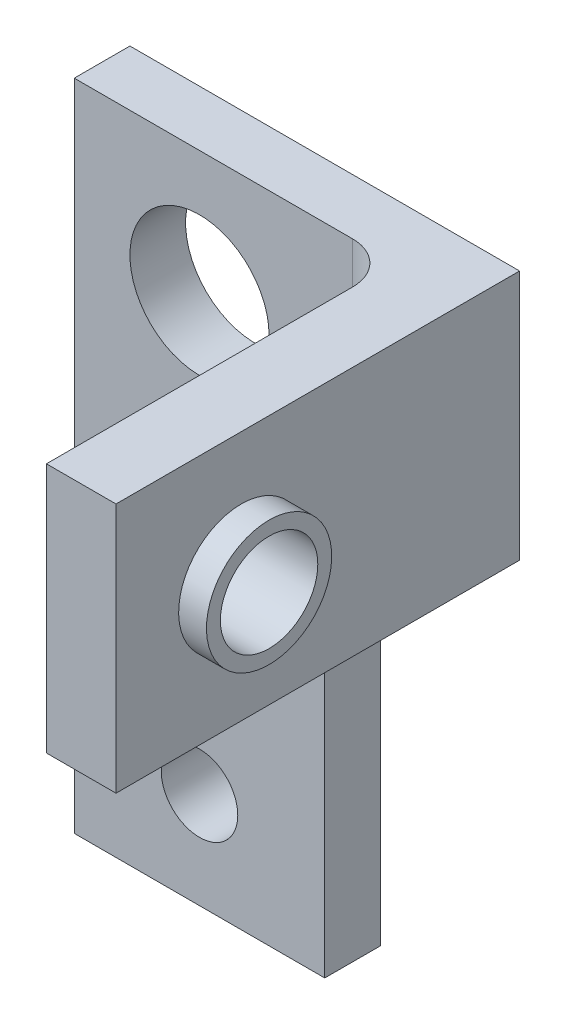
SolidWorks part; units mm, degrees
ref_plane "Front Plane" through (0, 0, 0) normal (0, 0, 1) x (1, 0, 0)
ref_plane "Top Plane" through (0, 0, 0) normal (0, 1, 0) x (1, 0, 0)
ref_plane "Right Plane" through (0, 0, 0) normal (1, 0, 0) x (0, 0, -1)
sketch "Sketch1" plane through (0, 0, 0) normal (0, 0, 1) x (1, 0, 0)
  line L1 (-4.5, 11) -> (4.5, 11)
  line L2 (-4.5, 11) -> (-4.5, -11)
  line L3 (-4.5, -11) -> (4.5, -11)
  line L4 (4.5, 11) -> (4.5, -11)
  point P0 (0, 0)
  dimension "D1" = 22
  dimension "D2" = 9
extrude "Boss-Extrude1" add sketch "Sketch1" along normal blind 2
sketch "Sketch3" plane through (0, 0, 2) normal (0, 0, 1) x (1, 0, 0)
  line L1 (-4.5, -11) -> (4.5, -11) construction
  line L2 (4.5, 11) -> (-4.5, 11) construction
  circle A0 centre (0, 6.5) radius 2.5
  circle A1 centre (0, -9) radius 1.375
  dimension "D1" = 5
  dimension "D2" = 2.75
  dimension "D3" = 2
  dimension "D4" = 4.5
extrude "Cut-Extrude1" cut sketch "Sketch3" against normal blind 2
sketch "Sketch4" plane through (4.5, 0, 0) normal (1, 0, 0) x (0, 0, -1)
  line L0 (0, -11) -> (0, 11) construction
  line L1 (-2, 11) -> (0, 11)
  line L2 (-2, 11) -> (-2, 2)
  line L3 (-2, 2) -> (0, 2)
  line L4 (0, 11) -> (0, 2)
  dimension "D1" = 9
extrude "Boss-Extrude2" add sketch "Sketch4" along normal blind 5
sketch "Sketch5" plane through (0, 0, 2) normal (0, 0, 1) x (1, 0, 0)
  line L0 (9.5, 2) -> (4.5, 2) construction
  line L1 (9.5, 11) -> (7, 11)
  line L2 (9.5, 11) -> (9.5, 2)
  line L3 (9.5, 2) -> (7, 2)
  line L4 (7, 11) -> (7, 2)
  dimension "D1" = 2.5
extrude "Boss-Extrude3" add sketch "Sketch5" along normal blind 12.5
sketch "Sketch6" plane through (7, 0, 0) normal (-1, 0, 0) x (0, 0, 1)
  line L0 (14.5, 2) -> (2, 2) construction
  line L1 (14.5, 11) -> (14.5, 2) construction
  circle A0 centre (10, 6.5) radius 1.75
  dimension "D1" = 3.5
  dimension "D2" = 4.5
  dimension "D3" = 4.5
extrude "Cut-Extrude2" cut sketch "Sketch6" against normal blind 2.5
sketch "Sketch14" plane through (9.5, 0, 0) normal (1, 0, 0) x (0, 0, -1)
  circle A0 centre (-10, 6.5) radius 2.25
  dimension "D1" = 4.5
extrude "Boss-Extrude6" add sketch "Sketch14" along normal blind 1
sketch "Sketch15" plane through (10.5, 0, 0) normal (1, 0, 0) x (0, 0, -1)
  line L0 (-14.5, 2) -> (-14.5, 11) construction
  line L1 (0, 11) -> (-14.5, 11) construction
  circle A0 centre (-10, 6.5) radius 1.75
  dimension "D3" = 3.5
  dimension "D1" = 4.5
  dimension "D2" = 4.5
extrude "Cut-Extrude4" cut sketch "Sketch15" against normal blind 1
sketch "Sketch16" plane through (7, 0, 0) normal (-1, 0, 0) x (0, 0, 1)
  circle A0 centre (10, 6.5) radius 2.25
  dimension "D1" = 4.5
extrude "Boss-Extrude7" add sketch "Sketch16" along normal blind 1
sketch "Sketch17" plane through (6, 0, 0) normal (-1, 0, 0) x (0, 0, 1)
  circle A0 centre (10, 6.5) radius 1.75
  dimension "D1" = 3.5
extrude "Cut-Extrude5" cut sketch "Sketch17" against normal blind 1
fillet "Fillet1" radius 1.5 1 edges at (7, 6.5, 2)
fillet "Fillet2" radius 1.5 1 edges at (4.5, 2, 1)
sketch "Sketch18" plane through (0, -11, 0) normal (0, -1, 0) x (1, 0, 0)
  line L1 (-4.5, 2) -> (4.5, 2)
  line L2 (-4.5, 2) -> (-4.5, 0)
  line L3 (-4.5, 0) -> (4.5, 0)
  line L4 (4.5, 2) -> (4.5, 0)
extrude "Boss-Extrude8" add sketch "Sketch18" along normal blind 1.5
